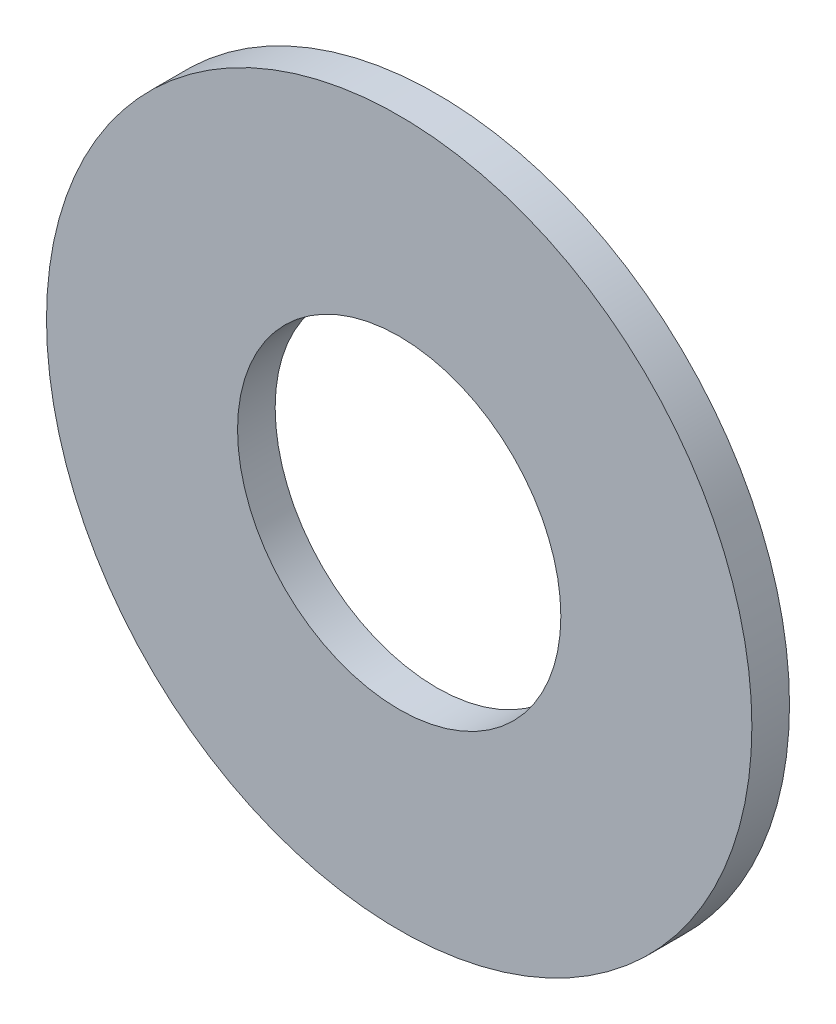
SolidWorks part; units mm, degrees
ref_plane "Front Plane" through (0, 0, 0) normal (0, 0, 1) x (1, 0, 0)
ref_plane "Top Plane" through (0, 0, 0) normal (0, 1, 0) x (1, 0, 0)
ref_plane "Right Plane" through (0, 0, 0) normal (1, 0, 0) x (0, 0, -1)
sketch "Sketch1" plane through (0, 0, 0) normal (0, 0, 1) x (1, 0, 0)
  circle A0 centre (0, 0) radius 4.3656
  circle A1 centre (0, 0) radius 9.525
  dimension "ID" = 8.7312
  dimension "OD" = 19.05
extrude "Extrude1" add sketch "Sketch1" against normal blind 1.016
